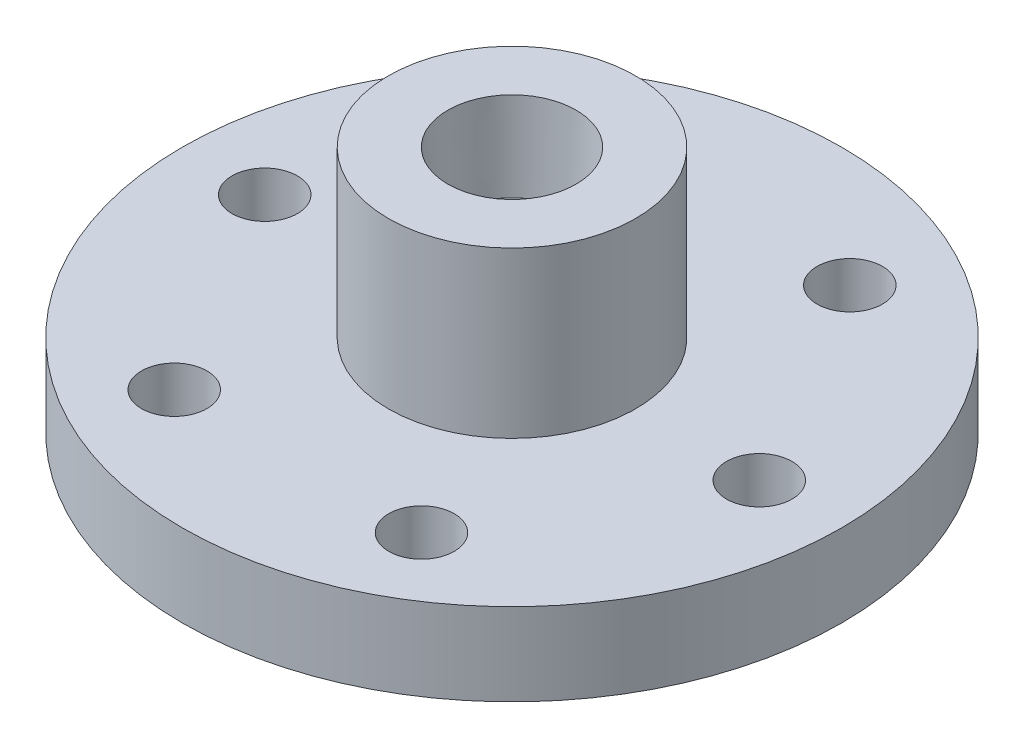
SolidWorks part; units mm, degrees
ref_plane "Front Plane" through (0, 0, 0) normal (0, 0, 1) x (1, 0, 0)
ref_plane "Top Plane" through (0, 0, 0) normal (0, 1, 0) x (1, 0, 0)
ref_plane "Right Plane" through (0, 0, 0) normal (1, 0, 0) x (0, 0, -1)
sketch "Sketch1" plane through (0, 0, 0) normal (0, 0, 1) x (1, 0, 0)
  line L0 (-12.827, 0) -> (-50.8, 0)
  line L1 (-50.8, 0) -> (-50.8, 12.7)
  line L2 (-50.8, 12.7) -> (-19.05, 12.7)
  line L3 (-19.05, 12.7) -> (-19.05, 38.1)
  line L4 (-19.05, 38.1) -> (0, 38.1)
  line L5 (0, 38.1) -> (0, 0)
  line L6 (0, 0) -> (-9.525, 0)
  line L7 (-9.525, 0) -> (-9.525, 2.54)
  line L8 (-9.525, 2.54) -> (-12.827, 2.54)
  line L9 (-12.827, 2.54) -> (-12.827, 0)
  dimension "D1" = 50.8
  dimension "D2" = 19.05
  dimension "D3" = 12.7
  dimension "D4" = 25.4
  dimension "D5" = 3.302
  dimension "D6" = 2.54
  dimension "D7" = 9.525
revolve "Revolve1" add sketch "Sketch1" angle 360 about L5
hole_wizard "3/8 (0.375) Diameter Hole1" positions "Sketch4" profile "Sketch6" hole size "3/8" standard "ANSI Inch" end condition through all
sketch "Sketch4" plane through (0, 38.1, 0) normal (0, 1, 0) x (1, 0, 0)
  point P0 (0, 0)
sketch "Sketch6" plane through (0, 38.1, 0) normal (1, 0, 0) x (0, 0, 1)
  line L0 (0, 0) -> (0, 38.1)
  line L1 (0, 38.1) -> (4.7625, 38.1)
  line L2 (4.7625, 38.1) -> (4.7625, 0)
  line L5 (4.7625, 0) -> (0, 0)
  line L11 (0, -6.35) -> (0, 107.95) construction
  dimension "Thru Hole Dia." = 9.525
  dimension "Thru Hole Depth" = 38.1
hole_wizard "1/2 NPT Tapped Hole1" positions "Sketch2" profile "Sketch3" size "1/2" standard "ANSI Inch"
sketch "Sketch2" plane through (0, 38.1, 0) normal (0, 1, 0) x (1, 0, 0)
  point P0 (0, 0)
sketch "Sketch3" plane through (0, 38.1, 0) normal (1, 0, 0) x (0, 0, 1)
  line L0 (0, 0) -> (0, 27.9705)
  line L1 (8.9281, 22.606) -> (0, 27.9705)
  line L2 (-8.9281, 22.606) -> (0, 27.9705) construction
  line L3 (8.9281, 22.606) -> (8.9281, 13.462)
  line L4 (8.9281, 13.462) -> (9.4797, 13.462)
  line L5 (9.4797, 13.462) -> (9.8828, 0)
  line L6 (-9.4797, 13.462) -> (-9.8828, 0) construction
  line L7 (9.8828, 0) -> (0, 0)
  line L8 (0, -6.35) -> (0, 107.95) construction
  line L11 (-8.9281, 13.462) -> (-9.4797, 13.462) construction
  dimension "Tap Drill Dia." = 17.8562
  dimension "Tap Drill Depth" = 22.606
  dimension "Thread Dia." = 19.7656
  dimension "Thread Angle" = 3.43
  dimension "Thread Depth" = 13.462
  dimension "Drill Angle" = 118
cosmetic thread "Hole Thread1" parameters "D1"=13.462, "D2"=21.3288
hole_wizard "3/8 Clearance Hole1" positions "Sketch7" profile "Sketch8" hole size "3/8" standard "ANSI Inch" end condition through all
sketch "Sketch7" plane through (0, 12.7, 0) normal (0, 1, 0) x (1, 0, 0)
  point P0 (38.1, 0)
  point P4 (0, 0)
  dimension "D1" = 38.1
sketch "Sketch8" plane through (38.1, 12.7, 0) normal (1, 0, 0) x (0, 0, 1)
  line L0 (0, 0) -> (0, 12.7)
  line L1 (0, 12.7) -> (5.0419, 12.7)
  line L2 (5.0419, 12.7) -> (5.0419, 0)
  line L5 (5.0419, 0) -> (0, 0)
  line L11 (0, -6.35) -> (0, 107.95) construction
  dimension "Thru Hole Dia." = 10.0838
  dimension "Thru Hole Depth" = 12.7
pattern_circular "CirPattern1" count 6 over 360 about axis through (0, 0, 0) along (0, 1, 0) of "3/8 Clearance Hole1"
